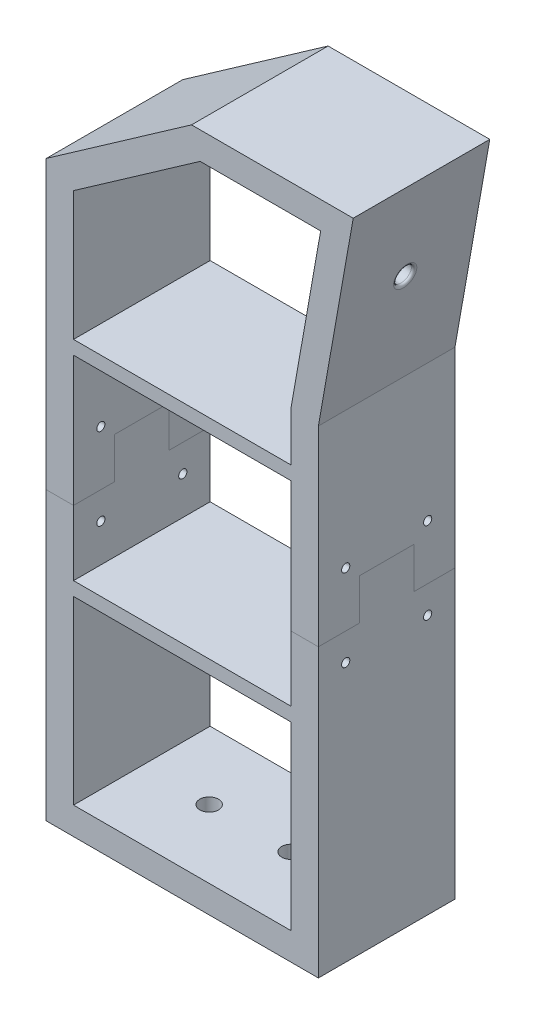
SolidWorks part; units mm, degrees
ref_plane "Front Plane" through (0, 0, 0) normal (0, 0, 1) x (1, 0, 0)
ref_plane "Top Plane" through (0, 0, 0) normal (0, 1, 0) x (1, 0, 0)
ref_plane "Right Plane" through (0, 0, 0) normal (1, 0, 0) x (0, 0, -1)
sketch "Sketch2" plane through (0, 0, 0) normal (0, 0, 1) x (1, 0, 0)
  line L8 (-40.5065, 0) -> (59.131, 0)
  line L12 (59.131, 0) -> (59.131, 175)
  line L14 (59.131, 175) -> (59.131, 265.8716) construction
  line L16 (49.131, 175.8749) -> (59.9525, 237.2467)
  line L17 (59.9525, 237.2467) -> (15.8403, 237.2467)
  line L18 (15.8403, 237.2467) -> (-30.5065, 204.7943)
  line L19 (0, 0) -> (0, 10) construction
  line L23 (-40.5065, 210) -> (-40.5065, 0)
  line L30 (59.131, 175) -> (71.87, 247.2467)
  line L35 (-30.5065, 204.7943) -> (-30.5065, 10)
  line L36 (71.87, 247.2467) -> (12.6873, 247.2467)
  line L37 (12.6873, 247.2467) -> (-40.5065, 210)
  line L38 (-30.5065, 10) -> (49.131, 10)
  line L39 (49.131, 10) -> (49.131, 175.8749)
  point P1 (9.131, 107.9897)
  dimension "D1" = 10
  dimension "D2" = 9.131
  dimension "D3" = 175
  dimension "D4" = 59.131
  dimension "D5" = 71.87
  dimension "D6" = 235
  dimension "D7" = 40.5065
  dimension "D8" = 210
  dimension "D9" = 10
extrude "Boss-Extrude1" add sketch "Sketch2" along normal blind 50
sketch "Sketch10" plane through (0, 10, 0) normal (0, 1, 0) x (1, 0, 0)
  line L0 (49.131, -25) -> (24.131, -25) construction
  line L1 (-30.869, -50) -> (-30.869, 0) construction
  line L2 (-30.5065, -50) -> (-30.5065, 0) construction
  line L3 (-30.5065, -25) -> (-5.8513, -25) construction
  line L5 (49.131, -50) -> (49.131, 0) construction
  circle A0 centre (-5.8513, -25) radius 3.425
  circle A1 centre (24.131, -25) radius 3.425
  dimension "D1" = 6.85
  dimension "D2" = 6.85
  dimension "D3" = 25.0177
  dimension "D4" = 55
extrude "Cut-Extrude5" cut sketch "Sketch10" against normal blind 10
sketch "Sketch11" plane through (0, 0, 50) normal (0, 0, 1) x (1, 0, 0)
  line L1 (-30.5065, 157.6357) -> (49.131, 157.6357)
  line L6 (-30.5065, 204.7943) -> (-30.5065, 10) construction
  line L7 (-30.5065, 81.1513) -> (-30.5065, 157.6357) construction
  line L9 (49.131, 157.6357) -> (49.131, 152.6357)
  line L10 (49.131, 152.6357) -> (-30.5065, 152.6357)
  line L11 (-30.5065, 152.6357) -> (-30.5065, 157.6357)
  line L12 (-30.5065, 81.1513) -> (49.131, 81.1513)
  line L13 (49.131, 81.1513) -> (49.131, 76.1513)
  line L14 (49.131, 76.1513) -> (-30.5065, 76.1513)
  line L15 (-30.5065, 76.1513) -> (-30.5065, 81.1513)
  line L16 (49.131, 10) -> (49.131, 175.8749) construction
  line L17 (-40.5065, 0) -> (59.131, 0) construction
  dimension "D1" = 5
  dimension "D2" = 5
  dimension "D3" = 76.1513
  dimension "D4" = 152.6357
extrude "Boss-Extrude3" add sketch "Sketch11" against normal blind 50
sketch "Sketch14" plane through (27.4212, -4.8351, 0) normal (0.9848, -0.1736, 0) x (0, 0, -1)
  line L0 (-25, 182.6093) -> (-25, 221.6093) construction
  line L1 (-50, 182.6093) -> (0, 182.6093) construction
  circle A0 centre (-25, 221.6093) radius 3.2
  dimension "D1" = 6.4
extrude "Cut-Extrude6" cut sketch "Sketch14" against normal blind 10
fillet "Fillet1" radius 1 1 edges at (66.4589, 216.5589, 25)
sketch "Sketch15" plane through (-40.5065, 0, 0) normal (-1, 0, 0) x (0, 0, 1)
  line L0 (0, 105) -> (15, 105)
  line L1 (0, 210) -> (0, 0) construction
  line L2 (15, 105) -> (15, 120)
  line L3 (15, 120) -> (35, 120)
  line L4 (35, 120) -> (35, 105)
  line L5 (35, 105) -> (50, 105)
  line L6 (50, 210) -> (50, 0) construction
  dimension "D1" = 15
  dimension "D2" = 35
  dimension "D3" = 15
split "Split1" trim tools "Sketch15" bodies to split 109 resulting bodies 112 113
sketch "Sketch16" plane through (-40.5065, 0, 0) normal (-1, 0, 0) x (0, 0, 1)
  line L0 (0, 105) -> (0, 95) construction
  line L1 (0, 105) -> (0, 0) construction
  line L2 (0, 95) -> (10, 95) construction
  line L3 (25, 120) -> (25, 0) construction
  line L4 (15, 120) -> (35, 120) construction
  line L5 (50, 0) -> (0, 0) construction
  circle A0 centre (10, 95) radius 1.5
  circle A1 centre (40, 95) radius 1.5
  dimension "D1" = 3
  dimension "D2" = 10
  dimension "D3" = 10
extrude "Cut-Extrude7" cut sketch "Sketch16" along direction (1, 0, 0) on the side against the normal up to surface (99.6375 mm away)
sketch "Sketch17" plane through (-40.5065, 0, 0) normal (-1, 0, 0) x (0, 0, 1)
  line L0 (50, 105) -> (50, 125) construction
  line L1 (50, 210) -> (50, 105) construction
  line L2 (50, 125) -> (40, 125) construction
  line L3 (25, 120) -> (25, 148.2299) construction
  line L4 (15, 120) -> (35, 120) construction
  circle A0 centre (40, 125) radius 1.5
  circle A1 centre (10, 125) radius 1.5
  dimension "D2" = 3
  dimension "D1" = 20
  dimension "D3" = 10
extrude "Cut-Extrude8" cut sketch "Sketch17" against normal up to surface (99.6375 mm away) up to face at (59.131, 126.25, 25)
